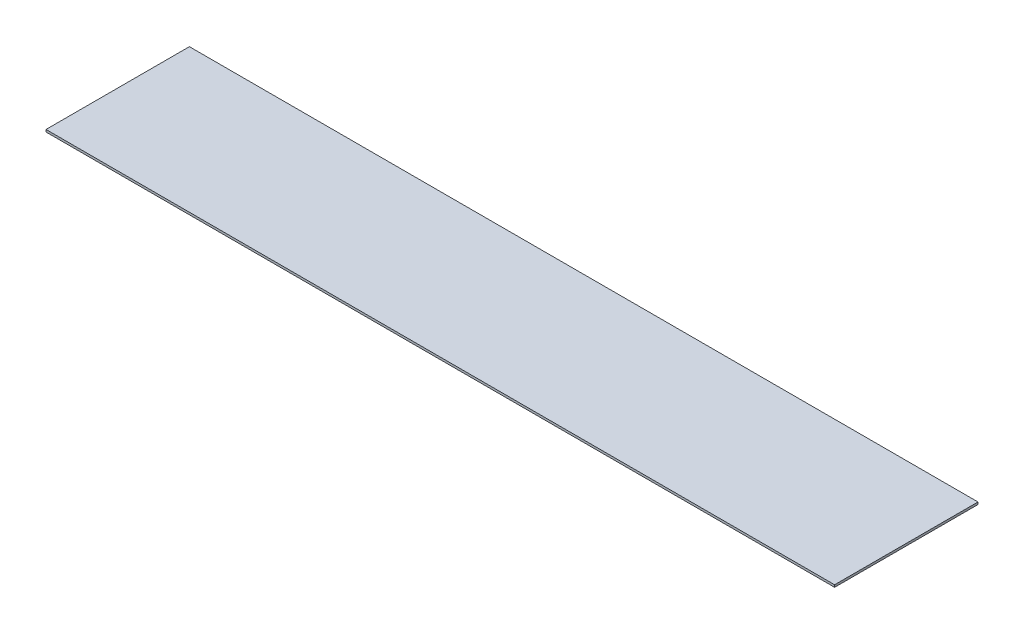
SolidWorks part; units mm, degrees
material "Nylon 6/10"
ref_plane "Front Plane" through (0, 0, 0) normal (0, 0, 1) x (1, 0, 0)
ref_plane "Top Plane" through (0, 0, 0) normal (0, 1, 0) x (1, 0, 0)
ref_plane "Right Plane" through (0, 0, 0) normal (1, 0, 0) x (0, 0, -1)
sketch "Sketch1" plane through (0, 0, 0) normal (0, 1, 0) x (1, 0, 0)
  line L1 (0, 0) -> (558.8, 0)
  line L2 (0, 0) -> (0, 101.6)
  line L3 (0, 101.6) -> (558.8, 101.6)
  line L4 (558.8, 0) -> (558.8, 101.6)
  dimension "D1" = 558.8
  dimension "D2" = 101.6
extrude "Boss-Extrude1" add sketch "Sketch1" along normal blind 1.5875
